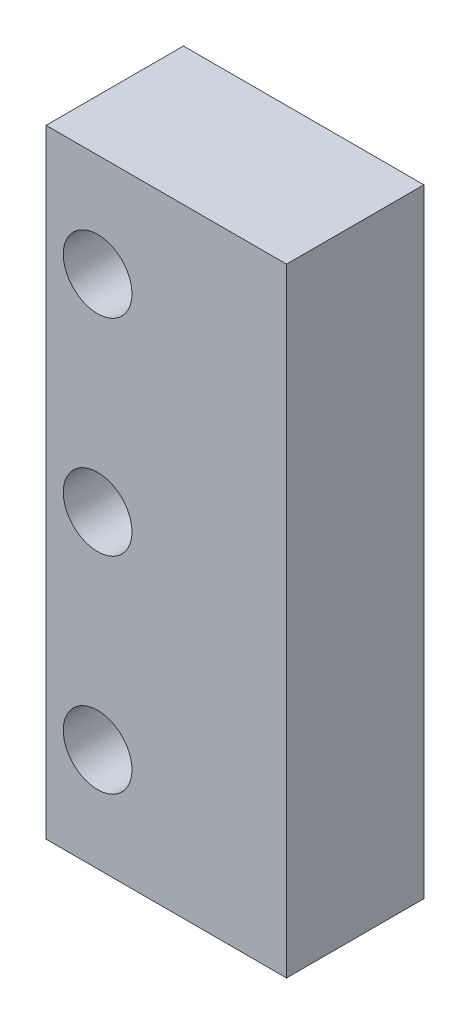
SolidWorks part; units mm, degrees
material "PET"
ref_plane "Front" through (0, 0, 0) normal (0, 0, 1) x (1, 0, 0)
ref_plane "Top" through (0, 0, 0) normal (0, 1, 0) x (1, 0, 0)
ref_plane "Right" through (0, 0, 0) normal (1, 0, 0) x (0, 0, -1)
sketch "Sketch1" plane through (0, 0, 0) normal (0, 0, 1) x (1, 0, 0)
  line L1 (0, 0) -> (-22.225, 0)
  line L2 (0, 0) -> (0, 57.15)
  line L3 (0, 57.15) -> (-22.225, 57.15)
  line L4 (-22.225, 0) -> (-22.225, 57.15)
  dimension "D1" = 57.15
  dimension "D2" = 22.225
extrude "Boss-Extrude1" add sketch "Sketch1" against normal blind 12.7
sketch "Sketch4" plane through (0, 0, 0) normal (0, 0, 1) x (1, 0, 0)
  line L0 (-17.4625, 47.625) -> (-17.4625, 9.525) construction
  line L4 (-22.225, 57.15) -> (-22.225, 0) construction
  line L5 (-17.4625, 47.625) -> (-17.4625, 57.15) construction
  line L6 (0, 57.15) -> (-22.225, 57.15) construction
  line L9 (-17.4625, 9.525) -> (-17.4625, 0) construction
  line L10 (-22.225, 0) -> (0, 0) construction
  point P0 (-17.4625, 47.625)
  point P2 (-17.4625, 28.575)
  point P4 (-17.4625, 9.525)
  dimension "D1" = 38.1
  dimension "D3" = 4.7625
hole_wizard "1/4 (0.25) Diameter Hole1" positions "Sketch4" profile "Sketch3" hole size "1/4" standard "ANSI Inch" end condition through all
sketch "Sketch3" plane through (-17.4625, 47.625, 0) normal (1, 0, 0) x (0, -1, 0)
  line L0 (0, 0) -> (0, 12.7)
  line L1 (0, 12.7) -> (3.175, 12.7)
  line L2 (3.175, 12.7) -> (3.175, 0)
  line L5 (3.175, 0) -> (0, 0)
  line L11 (0, -6.35) -> (0, 107.95) construction
  dimension "Thru Hole Dia." = 6.35
  dimension "Thru Hole Depth" = 12.7
